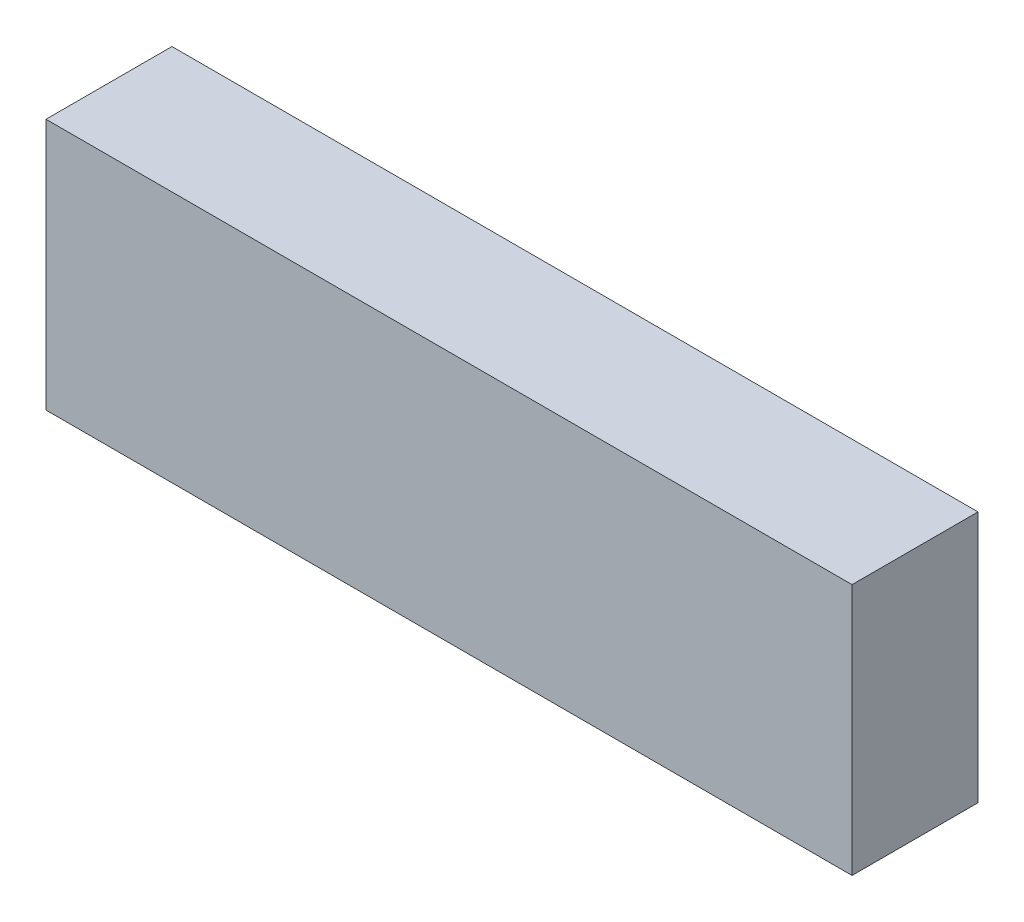
SolidWorks part; units mm, degrees
ref_plane "Plan de face" through (0, 0, 0) normal (0, 0, 1) x (1, 0, 0)
ref_plane "Plan de dessus" through (0, 0, 0) normal (0, 1, 0) x (1, 0, 0)
ref_plane "Plan de droite" through (0, 0, 0) normal (1, 0, 0) x (0, 0, -1)
sketch "Esquisse1" plane through (0, 0, 0) normal (0, 0, 1) x (1, 0, 0)
  line L1 (0, 0) -> (160, 0)
  line L2 (0, 0) -> (0, 50)
  line L3 (0, 50) -> (160, 50)
  line L4 (160, 0) -> (160, 50)
  dimension "D1" = 160
  dimension "D2" = 50
extrude "Boss.-Extru.1" add sketch "Esquisse1" along normal blind 25
